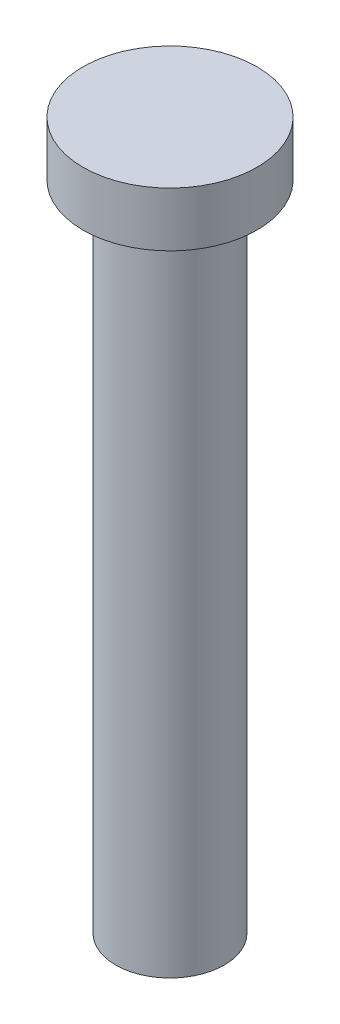
SolidWorks part; units mm, degrees
ref_plane "Front Plane" through (0, 0, 0) normal (0, 0, 1) x (1, 0, 0)
ref_plane "Top Plane" through (0, 0, 0) normal (0, 1, 0) x (1, 0, 0)
ref_plane "Right Plane" through (0, 0, 0) normal (1, 0, 0) x (0, 0, -1)
sketch "Sketch1" plane through (0, 0, 0) normal (0, 1, 0) x (1, 0, 0)
  circle A0 centre (0, 0) radius 2.5
  dimension "D1" = 5
extrude "Boss-Extrude1" add sketch "Sketch1" along normal blind 30
sketch "Sketch2" plane through (0, 30, 0) normal (0, 1, 0) x (1, 0, 0)
  circle A0 centre (0, 0) radius 4
  dimension "D1" = 8
extrude "Boss-Extrude2" add sketch "Sketch2" along normal blind 2.5
chamfer "Chamfer1" distance 1 angle 45 1 edges at (0, 30, 2.5)
